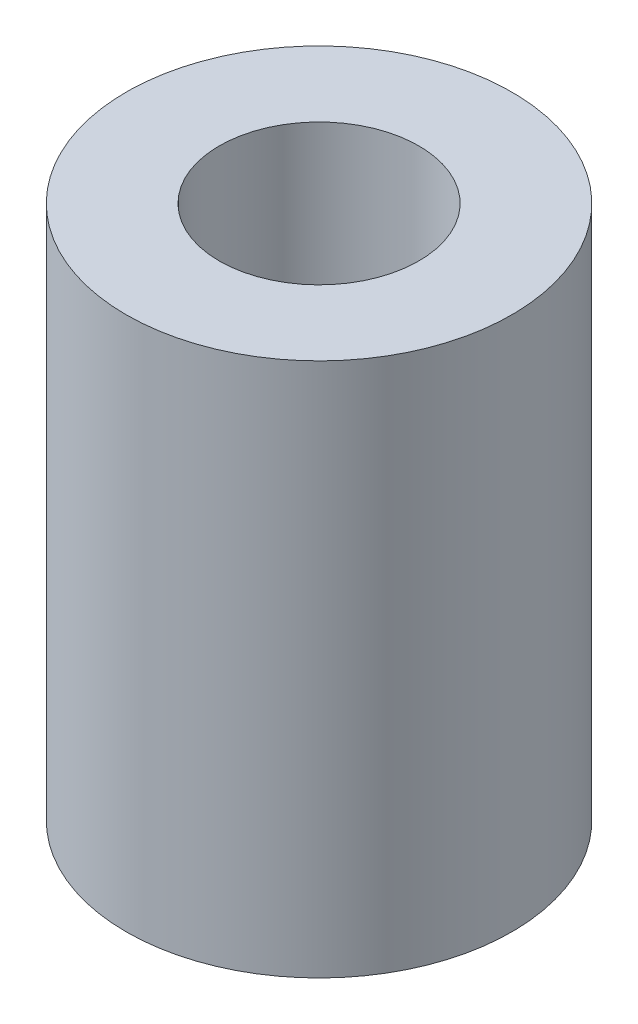
SolidWorks part; units mm, degrees
ref_plane "Front" through (0, 0, 0) normal (0, 0, 1) x (1, 0, 0)
ref_plane "Top" through (0, 0, 0) normal (0, 1, 0) x (1, 0, 0)
ref_plane "Right" through (0, 0, 0) normal (1, 0, 0) x (0, 0, -1)
sketch "Sketch1" plane through (0, 0, 0) normal (0, 1, 0) x (1, 0, 0)
  circle A0 centre (0, 0) radius 6.2611
  circle A1 centre (0, 0) radius 3.2385
  dimension "D1" = 12.5222
  dimension "D2" = 6.477
extrude "Boss-Extrude1" add sketch "Sketch1" along normal blind 17.3482
